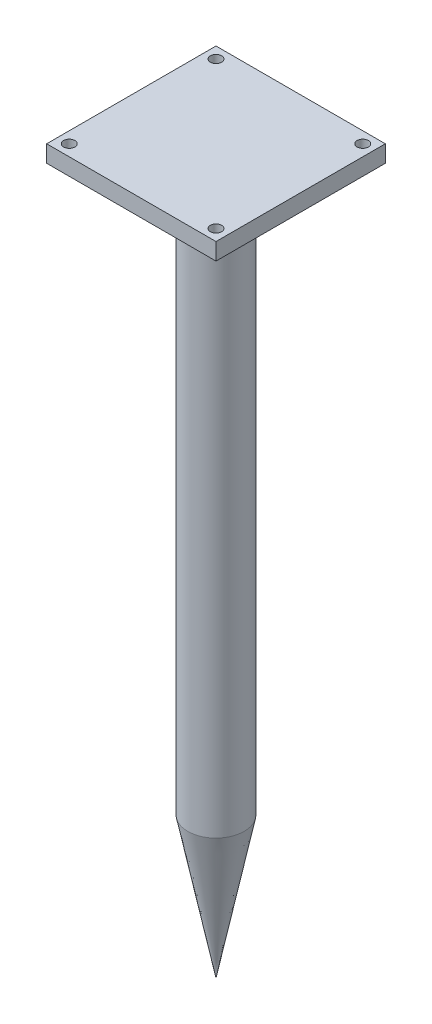
SolidWorks part; units mm, degrees
ref_plane "Front Plane" through (0, 0, 0) normal (0, 0, 1) x (1, 0, 0)
ref_plane "Top Plane" through (0, 0, 0) normal (0, 1, 0) x (1, 0, 0)
ref_plane "Right Plane" through (0, 0, 0) normal (1, 0, 0) x (0, 0, -1)
sketch "Sketch1" plane through (0, 0, 0) normal (0, 1, 0) x (1, 0, 0)
  circle A0 centre (0, 0) radius 5
  dimension "D1" = 10
extrude "Boss-Extrude1" add sketch "Sketch1" along normal blind 100
sketch "Sketch3" plane through (0, 100, 0) normal (0, 1, 0) x (1, 0, 0)
  line L1 (-15, 15) -> (15, 15)
  line L2 (-15, 15) -> (-15, -15)
  line L3 (-15, -15) -> (15, -15)
  line L4 (15, 15) -> (15, -15)
  line L5 (-15, 15) -> (15, -15) construction
  line L6 (-15, -15) -> (15, 15) construction
  point P0 (0, 0)
  dimension "D1" = 30
  dimension "D2" = 30
extrude "Boss-Extrude3" add sketch "Sketch3" along normal blind 3
sketch "Sketch4" plane through (0, 103, 0) normal (0, 1, 0) x (1, 0, 0)
  line L0 (0, 0) -> (0, 5.021) construction
  line L1 (-4.0734, 0) -> (3.7905, 0) construction
  line L2 (-15, 15) -> (-15, -15) construction
  line L4 (15, 15) -> (-15, 15) construction
  circle A0 centre (-13, 13) radius 1
  circle A1 centre (13, 13) radius 1
  circle A2 centre (13, -13) radius 1
  circle A3 centre (-13, -13) radius 1
  dimension "D1" = 2
  dimension "D2" = 2
  dimension "D3" = 2
extrude "Cut-Extrude1" cut sketch "Sketch4" against normal up to surface (3 mm away) up to face at (0, 100, 5)
sketch "Sketch5" plane through (0, 0, 0) normal (1, 0, 0) x (0, 0, -1)
  line L0 (0, 0) -> (0, -25)
  line L1 (0, -25) -> (5, 0)
  line L2 (5, 0) -> (0, 0)
  dimension "D1" = 25
revolve "Revolve1" add sketch "Sketch5" angle 360 about L0
